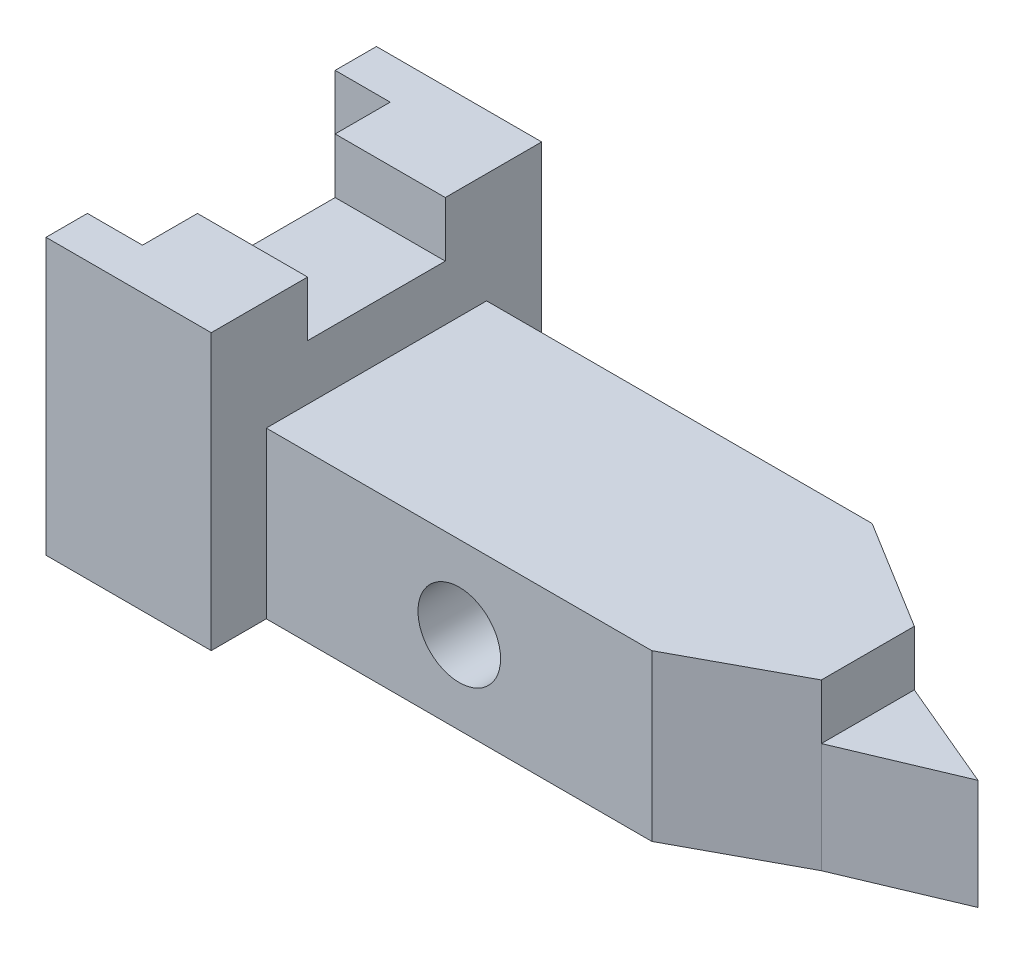
SolidWorks part; units mm, degrees
ref_plane "Front Plane" through (0, 0, 0) normal (0, 0, 1) x (1, 0, 0)
ref_plane "Top Plane" through (0, 0, 0) normal (0, 1, 0) x (1, 0, 0)
ref_plane "Right Plane" through (0, 0, 0) normal (1, 0, 0) x (0, 0, -1)
sketch "Sketch1" plane through (0, 0, 0) normal (0, 1, 0) x (1, 0, 0)
  line L1 (-30, 8.982) -> (0, 8.982)
  line L2 (-30, 8.982) -> (-30, -51.018)
  line L3 (-30, -51.018) -> (0, -51.018)
  line L4 (0, 8.982) -> (0, -51.018)
  dimension "D1" = 30
  dimension "D2" = 60
extrude "Boss-Extrude1" add sketch "Sketch1" against normal blind 50
sketch "Sketch2" plane through (0, 0, 0) normal (1, 0, 0) x (0, 0, -1)
  line L0 (-21.018, -50) -> (-41.018, -50)
  line L1 (-51.018, -50) -> (8.982, -50) construction
  line L2 (-21.018, -50) -> (-1.018, -50)
  line L3 (-41.018, -50) -> (-41.018, -20)
  line L4 (-41.018, -20) -> (-1.018, -20)
  line L5 (-1.018, -20) -> (-1.018, -50)
  dimension "D1" = 20
  dimension "D2" = 30
extrude "Boss-Extrude2" add sketch "Sketch2" along normal blind 90
sketch "Sketch3" plane through (0, 0, 41.018) normal (0, 0, 1) x (1, 0, 0)
  line L0 (0, -50) -> (0, -35) construction
  line L1 (0, -20) -> (0, -50) construction
  line L2 (0, -35) -> (35.0369, -35) construction
  circle A0 centre (35.0369, -35) radius 7.5
  dimension "D1" = 15
extrude "Cut-Extrude1" cut sketch "Sketch3" against normal blind 90
sketch "Sketch4" plane through (0, -20, 0) normal (0, 1, 0) x (1, 0, 0)
  line L0 (0, -41.018) -> (35, -41.018) construction
  line L1 (90, -41.018) -> (0, -41.018) construction
  line L2 (35, -1.018) -> (70, -1.018) construction
  line L3 (90, -1.018) -> (0, -1.018) construction
  line L4 (70, -1.018) -> (90, -13.3531)
  line L5 (90, -1.018) -> (90, -41.018) construction
  line L6 (70, -41.018) -> (90, -30.2331)
  line L7 (70, -1.018) -> (90, -1.018)
  line L8 (90, -1.018) -> (90, -13.3531)
  line L9 (90, -41.018) -> (90, -30.2331)
  line L10 (70, -41.018) -> (90, -41.018)
  dimension "D1" = 35
  dimension "D2" = 35
  dimension "D3" = 60
extrude "Cut-Extrude2" cut sketch "Sketch4" against normal blind 90
sketch "Sketch5" plane through (90, 0, 0) normal (1, 0, 0) x (0, 0, -1)
  line L0 (-30.2331, -20) -> (-30.2331, -30)
  line L1 (-30.2331, -20) -> (-30.2331, -50) construction
  line L2 (-30.2331, -30) -> (-13.3531, -30)
  line L3 (-13.3531, -50) -> (-13.3531, -20) construction
  line L4 (-13.3531, -30) -> (-13.3531, -50)
  line L5 (-13.3531, -50) -> (-30.2331, -50)
  line L6 (-30.2331, -50) -> (-30.2331, -30)
  line M2 (-30.2331, -50) -> (-13.3531, -50)
  line M3 (-13.3531, -50) -> (-13.3531, -20)
  line M5 (-30.2331, -20) -> (-30.2331, -50)
  dimension "D1" = 10
extrude "Boss-Extrude3" add sketch "Sketch5" along normal blind 20 contours L2 M5 M2 M3
sketch "Sketch6" plane through (0, -30, 0) normal (0, 1, 0) x (1, 0, 0)
  line L0 (90, -13.3531) -> (110, -21.7931)
  line L1 (110, -30.2331) -> (110, -13.3531) construction
  line L2 (110, -21.7931) -> (90, -30.2331)
  line L3 (90, -30.2331) -> (90, -13.3531)
  line L4 (90, -13.3531) -> (110, -13.3531)
  line L5 (110, -13.3531) -> (110, -21.7931)
  line L6 (90, -30.2331) -> (110, -30.2331)
  line L7 (110, -30.2331) -> (110, -21.7931)
  line M5 (90, -30.2331) -> (110, -30.2331)
  line M6 (110, -30.2331) -> (110, -13.3531)
  line M7 (110, -13.3531) -> (90, -13.3531)
extrude "Cut-Extrude3" cut sketch "Sketch6" against normal blind 20 contours L0 M7 M6 | L2 M6 M5
sketch "Sketch7" plane through (0, 0, 0) normal (0, 1, 0) x (1, 0, 0)
  line L2 (0, -51.018) -> (0, 8.982) construction
  line L3 (-30, -51.018) -> (0, -51.018)
  line L4 (0, -51.018) -> (0, -33.518)
  line L8 (-30, 8.982) -> (-30, -51.018) construction
  line L11 (-20, -33.518) -> (-20, -43.5015)
  line L12 (-20, -43.5015) -> (-30, -43.5015)
  line L15 (-20, -43.5015) -> (-20, -33.518)
  line L17 (-20, -8.518) -> (-20, 1.482)
  line L18 (-20, -33.518) -> (0, -33.518)
  line L19 (0, -33.518) -> (0, -8.518)
  line L20 (0, -8.518) -> (-20, -8.518)
  line L21 (-30, 1.482) -> (-30, -43.5015)
  line L22 (0, -8.518) -> (0, -33.518)
  line L23 (-20, 1.482) -> (-30, 1.482)
  line M16 (-30, 8.982) -> (-30, -51.018)
  line M18 (0, -51.018) -> (0, 8.982)
  dimension "D2" = 17.5
  dimension "D3" = 20
  dimension "D4" = 10
extrude "Cut-Extrude4" cut sketch "Sketch7" against normal blind 10 contours L17 L23 L12 L11 L18 L20 M16 M18
sketch "Sketch8" plane through (0, -10, 0) normal (0, 1, 0) x (1, 0, 0)
  line L1 (-30, 1.482) -> (-20, 1.482)
  line L2 (-30, 1.482) -> (-30, -43.5015)
  line L3 (-30, -43.5015) -> (-20, -43.5015)
  line L4 (-20, 1.482) -> (-20, -43.5015)
extrude "Cut-Extrude5" cut sketch "Sketch8" against normal blind 50
